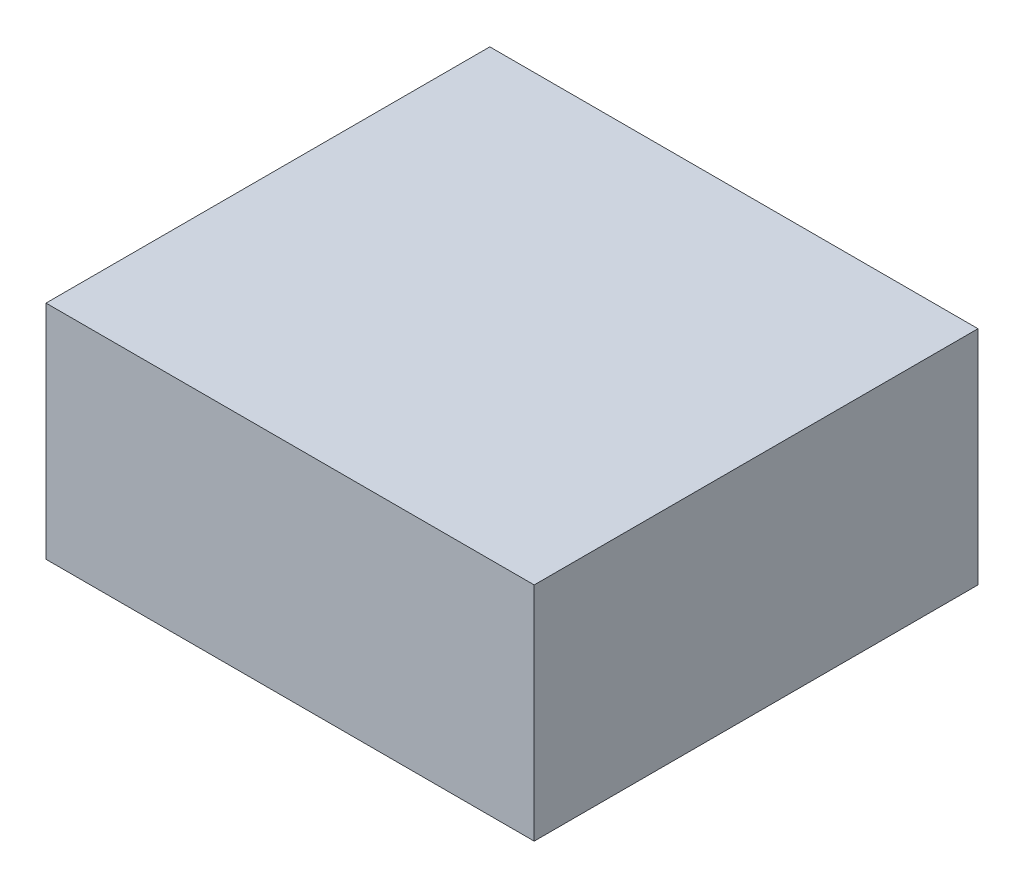
SolidWorks part; units mm, degrees
ref_plane "Plan de face" through (0, 0, 0) normal (0, 0, 1) x (1, 0, 0)
ref_plane "Plan de dessus" through (0, 0, 0) normal (0, 1, 0) x (1, 0, 0)
ref_plane "Plan de droite" through (0, 0, 0) normal (1, 0, 0) x (0, 0, -1)
sketch "Esquisse1" plane through (0, 0, 0) normal (0, 0, 1) x (1, 0, 0)
  line L1 (-55, -25) -> (55, -25)
  line L2 (-55, -25) -> (-55, 25)
  line L3 (-55, 25) -> (55, 25)
  line L4 (55, -25) -> (55, 25)
  line L5 (-55, -25) -> (55, 25) construction
  line L6 (-55, 25) -> (55, -25) construction
  point P0 (0, 0)
  dimension "D1" = 110
  dimension "D2" = 50
extrude "Boss.-Extru.1" add sketch "Esquisse1" along normal blind 100
